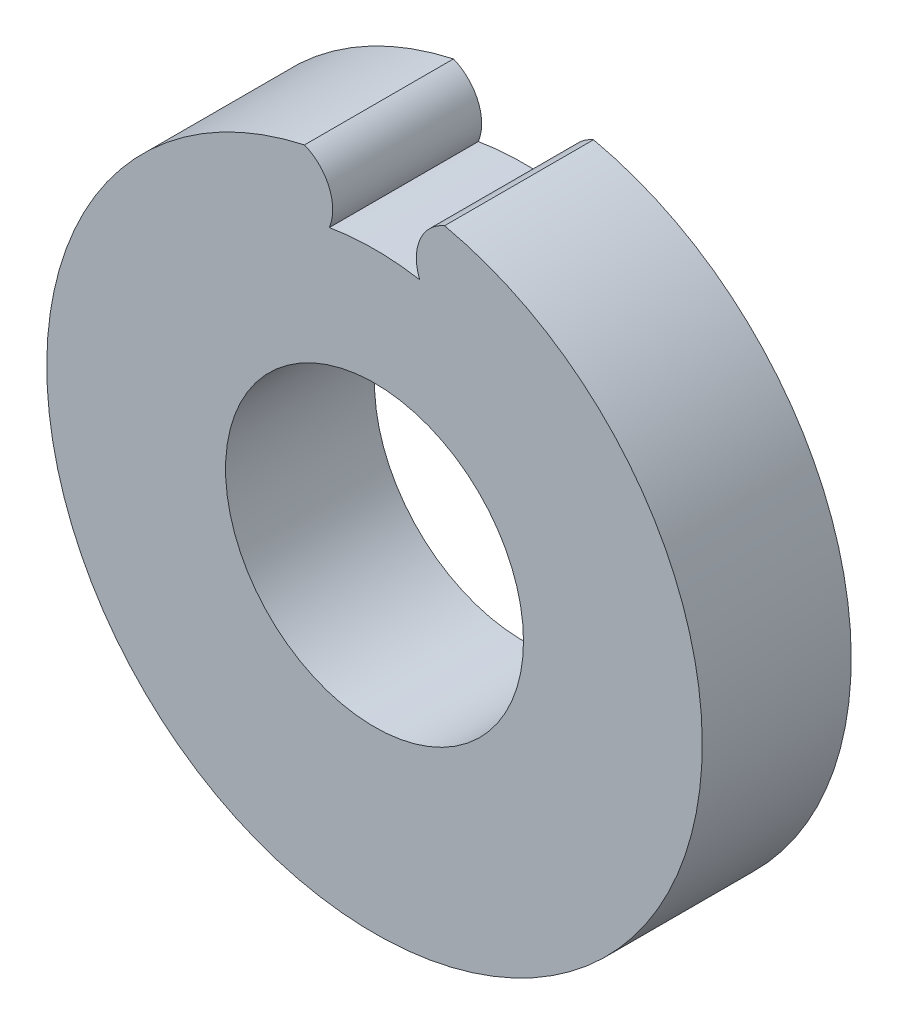
SolidWorks part; units mm, degrees
ref_plane "Front Plane" through (0, 0, 0) normal (0, 0, 1) x (1, 0, 0)
ref_plane "Top Plane" through (0, 0, 0) normal (0, 1, 0) x (1, 0, 0)
ref_plane "Right Plane" through (0, 0, 0) normal (1, 0, 0) x (0, 0, -1)
sketch "Sketch1" plane through (0, 0, 0) normal (0, 0, 1) x (1, 0, 0)
  circle A0 centre (0, 0) radius 6
  circle A1 centre (0, 0) radius 13.2
extrude "Boss-Extrude1" add sketch "Sketch1" along normal blind 6
sketch "Sketch2" plane through (0, 0, 6) normal (0, 0, 1) x (1, 0, 0)
  line L0 (0, 0) -> (0, 15.2) construction
  line L1 (-1.8199, 15.2) -> (0, 0) construction
  line L2 (1.8199, 15.2) -> (0, 0) construction
  arc A0 (-1.8199, 12) -> (1.8199, 12) centre (0, 0) cw
  arc A1 (-2.8199, 12.8953) -> (2.8199, 12.8953) centre (0, 0) cw
  arc A2 (-1.8199, 10.512) -> (1.8199, 10.512) centre (0, 0) cw
  arc A3 (-2.8199, 12.8953) -> (-1.8199, 10.512) centre (-3.5115, 11.2036) cw
  arc A4 (2.8199, 12.8953) -> (1.8199, 10.512) centre (3.5115, 11.2036) ccw
extrude "Cut-Extrude1" cut sketch "Sketch2" against normal through all contours A1 A4 A2 A3
